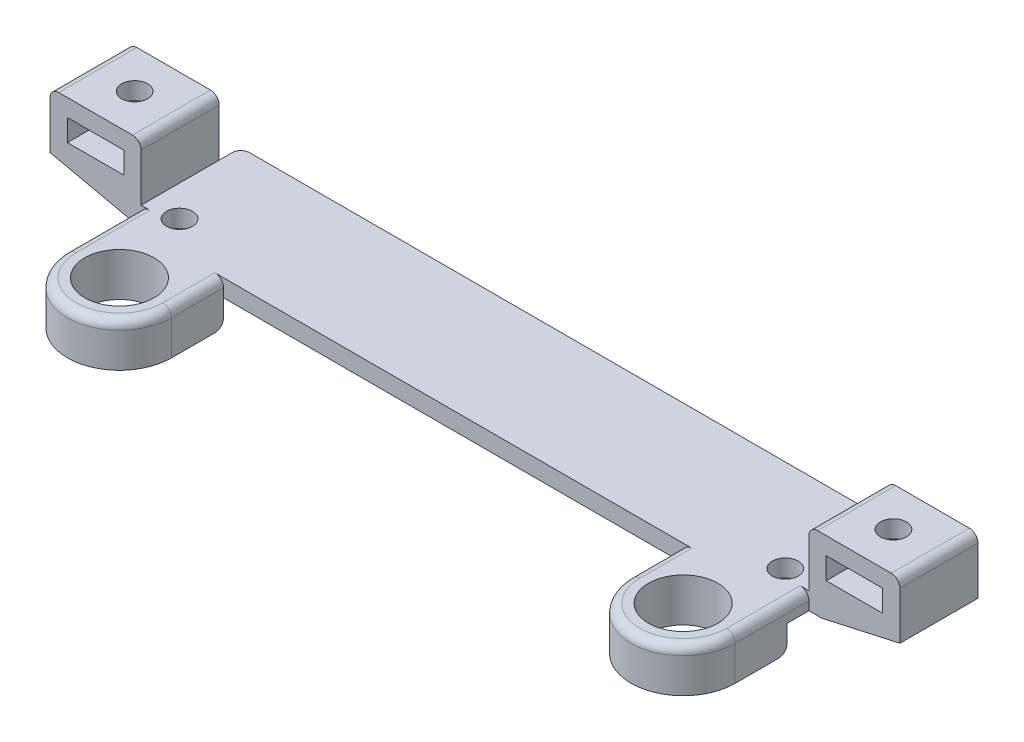
SolidWorks part; units mm, degrees
ref_plane "Front Plane" through (0, 0, 0) normal (0, 0, 1) x (1, 0, 0)
ref_plane "Top Plane" through (0, 0, 0) normal (0, 1, 0) x (1, 0, 0)
ref_plane "Right Plane" through (0, 0, 0) normal (1, 0, 0) x (0, 0, -1)
sketch "Sketch1" plane through (0, 0, 0) normal (0, 1, 0) x (1, 0, 0)
  line L5 (-91.7538, 1.2704) -> (-14.7538, 1.2704)
  line L6 (-91.7538, 1.2704) -> (-91.7538, -12.7296)
  line L7 (-91.7538, -12.7296) -> (-14.7538, -12.7296)
  line L8 (-14.7538, 1.2704) -> (-14.7538, -12.7296)
extrude "Boss-Extrude1" add sketch "Sketch1" along normal blind 2 contours L6 L5 L8 L7
sketch "Sketch3" plane through (-91.7538, 0, 0) normal (-1, 0, 0) x (0, 0, 1)
  line L0 (5.7296, 2) -> (1.2296, 2) construction
  line L1 (-1.2704, 2) -> (12.7296, 2) construction
  line L2 (5.7296, 2) -> (10.2296, 2) construction
  line L3 (10.2296, 2) -> (10.2296, 0) construction
  line L4 (-1.2704, 0) -> (12.7296, 0) construction
  line L6 (1.2296, 2) -> (10.2296, 2)
  line L7 (1.2296, 2) -> (1.2296, 0)
  line L8 (1.2296, 0) -> (10.2296, 0)
  line L9 (10.2296, 2) -> (10.2296, 0)
extrude "Boss-Extrude2" add sketch "Sketch3" along normal blind 10.5 contours L7 L6 L9 L8
sketch "Sketch4" plane through (-14.7538, 0, 0) normal (1, 0, 0) x (0, 0, -1)
  line L0 (-5.7296, 2) -> (-10.2296, 2) construction
  line L1 (1.2704, 2) -> (-12.7296, 2) construction
  line L2 (-10.2296, 2) -> (-10.2296, 0) construction
  line L3 (-5.7296, 2) -> (-1.2296, 2) construction
  line L5 (-10.2296, 2) -> (-1.2296, 2)
  line L6 (-10.2296, 2) -> (-10.2296, 0)
  line L7 (-10.2296, 0) -> (-1.2296, 0)
  line L8 (-1.2296, 2) -> (-1.2296, 0)
extrude "Boss-Extrude3" add sketch "Sketch4" along normal blind 10.5 contours L6 L5 L8 L7
sketch "Sketch5" plane through (0, 2, 0) normal (0, 1, 0) x (1, 0, 0)
  line L9 (-91.7538, -1.2296) -> (-102.2538, -1.2296)
  line L10 (-91.7538, -1.2296) -> (-91.7538, -10.2296)
  line L11 (-91.7538, -10.2296) -> (-102.2538, -10.2296)
  line L12 (-102.2538, -1.2296) -> (-102.2538, -10.2296)
  line L13 (-14.7538, -10.2296) -> (-4.2538, -10.2296)
  line L14 (-14.7538, -10.2296) -> (-14.7538, -1.2296)
  line L15 (-14.7538, -1.2296) -> (-4.2538, -1.2296)
  line L16 (-4.2538, -10.2296) -> (-4.2538, -1.2296)
extrude "Boss-Extrude4" add sketch "Sketch5" along normal blind 6.5
sketch "Sketch6" plane through (0, 0, 10.2296) normal (0, 0, 1) x (1, 0, 0)
  line L0 (-14.7538, 2) -> (-4.2538, 8.5) construction
  line L5 (-102.2538, 8.5) -> (-91.7538, 2) construction
  line L6 (-12.7538, 6.5) -> (-6.2538, 4) construction
  line L7 (-12.7538, 6.5) -> (-6.2538, 6.5)
  line L12 (-12.7538, 6.5) -> (-12.7538, 4)
  line L13 (-12.7538, 4) -> (-6.2538, 4)
  line L14 (-6.2538, 6.5) -> (-6.2538, 4)
  line L15 (-100.2538, 6.5) -> (-93.7538, 4) construction
  line L16 (-100.2538, 6.5) -> (-93.7538, 6.5)
  line L17 (-100.2538, 6.5) -> (-100.2538, 4)
  line L18 (-100.2538, 4) -> (-93.7538, 4)
  line L19 (-93.7538, 6.5) -> (-93.7538, 4)
  point P16 (-9.5038, 5.25)
  point P17 (-97.0038, 5.25)
  point P18 (-9.5038, 5.25)
  point P19 (-97.0038, 5.25)
extrude "Cut-Extrude1" cut sketch "Sketch6" against normal up to surface (9 mm away) up to face at (-10.5538, 3.8, 1.2296)
sketch "Sketch8" plane through (0, 8.5, 0) normal (0, 1, 0) x (1, 0, 0)
  line L0 (-53.2538, 0.6204) -> (-90.7188, 0.6204) construction
  line L1 (-53.2538, 0.6204) -> (-15.7888, 0.6204) construction
  line L2 (-90.7188, 0.6204) -> (-90.7188, -12.0796) construction
  line L3 (-90.7188, -12.0796) -> (-15.7888, -12.0796) construction
  line L4 (-15.7888, -12.0796) -> (-15.7888, 0.6204) construction
  line L5 (-18.3288, -9.3796) -> (-88.1788, -9.3796) construction
  line L6 (-53.2538, 0.6204) -> (-53.2538, -9.3796) construction
  line L7 (-53.2538, -9.3796) -> (-53.2538, -12.0796) construction
  line L8 (-91.7538, 1.2704) -> (-14.7538, 1.2704) construction
  line L9 (-91.7538, 1.2704) -> (-14.7538, 1.2704) construction
  line L10 (-14.7538, 1.2704) -> (-14.7538, -1.2296) construction
  circle A0 centre (-88.1788, -9.3796) radius 1.5
  circle A1 centre (-18.3288, -9.3796) radius 1.5
  circle A2 centre (-97.0038, -5.7296) radius 1.5
  circle A3 centre (-9.5038, -5.7296) radius 1.5
  point P11 (-97.0038, -5.7296)
  point P16 (-9.5038, -5.7296)
extrude "Cut-Extrude2" cut sketch "Sketch8" against normal up to surface (8.5 mm away) up to face at (-53.2538, 0, 5.7296)
sketch "Sketch10" plane through (0, 0, 0) normal (0, -1, 0) x (-1, 0, 0)
  line L0 (102.2538, -10.2296) -> (102.2538, -8.7296) construction
  line L1 (102.2538, -1.2296) -> (102.2538, -10.2296) construction
  line L2 (102.2538, -1.2296) -> (102.2538, -2.7296) construction
  line L3 (91.7538, -10.2296) -> (91.7538, -8.7296) construction
  line L4 (14.7538, -10.2296) -> (14.7538, -8.7296) construction
  line L5 (102.2538, -8.7296) -> (93.2538, -8.7296)
  line L6 (102.2538, -8.7296) -> (102.2538, -2.7296)
  line L7 (102.2538, -2.7296) -> (93.2538, -2.7296)
  line L9 (4.2538, -10.2296) -> (4.2538, -8.7296) construction
  line L10 (4.2538, -10.2296) -> (4.2538, -1.2296) construction
  line L11 (4.2538, -1.2296) -> (4.2538, -2.7296) construction
  line L12 (93.2538, -2.7296) -> (93.2538, -8.7296)
  line L13 (4.2538, -8.7296) -> (13.2538, -8.7296)
  line L14 (4.2538, -8.7296) -> (4.2538, -2.7296)
  line L15 (4.2538, -2.7296) -> (13.2538, -2.7296)
  line L17 (13.2538, -2.7296) -> (13.2538, -8.7296)
  line L18 (14.7538, -2.7296) -> (14.7538, -1.2296) construction
  line L19 (91.7538, -2.7296) -> (91.7538, -1.2296) construction
  point P34 (93.2538, -5.7296)
  point P40 (13.2538, -5.7296)
extrude "Cut-Extrude4" cut sketch "Sketch10" against normal blind 2
chamfer "Chamfer1" distance 9 distance2 2 4 edges at (-102.2538, 0, 1.9796) (-4.2538, 0, 9.4796) (-4.2538, 0, 1.9796) (-102.2538, 0, 9.4796)
sketch "Sketch12" plane through (0, 2, 0) normal (0, 1, 0) x (1, 0, 0)
  line L1 (-91.7538, -12.7296) -> (-14.7538, -12.7296) construction
  line L3 (-26.7538, -12.7296) -> (-14.7538, -12.7296)
  line L4 (-91.7538, -12.7296) -> (-91.7538, -18.7296)
  line L5 (-91.7538, -12.7296) -> (-79.7538, -12.7296)
  line L6 (-79.7538, -18.7296) -> (-79.7538, -12.7296)
  line L7 (-26.7538, -18.7296) -> (-26.7538, -12.7296)
  line L8 (-14.7538, -18.7296) -> (-14.7538, -12.7296)
  arc A0 (-91.7538, -18.7296) -> (-79.7538, -18.7296) centre (-85.7538, -18.7296) ccw
  arc A1 (-26.7538, -18.7296) -> (-14.7538, -18.7296) centre (-20.7538, -18.7296) ccw
extrude "Boss-Extrude5" add sketch "Sketch12" against normal blind 5
sketch "Sketch13" plane through (0, 2, 0) normal (0, 1, 0) x (1, 0, 0)
  circle A0 centre (-85.7538, -18.7296) radius 4
  circle A1 centre (-20.7538, -18.7296) radius 4
extrude "Cut-Extrude5" cut sketch "Sketch13" against normal up to surface (5 mm away) up to face at (-85.7538, -3, 17.2296)
fillet "Fillet3" radius 1 14 edges at (-102.2538, 8.5, 5.7296) (-91.7538, 8.5, 5.7296) (-91.7538, 1, -1.2704) (-14.7538, 1, -1.2704) (-26.7538, 2, 15.7296) (-14.7538, 2, 14.4796) (-91.7538, 2, 14.4796) (-79.7538, 2, 15.7296) (-20.7538, 2, 24.7296) (-85.7538, 2, 24.7296) (-85.7538, -3, 12.7296) (-20.7538, -3, 12.7296) (-14.7538, 8.5, 5.7296) (-4.2538, 8.5, 5.7296)
